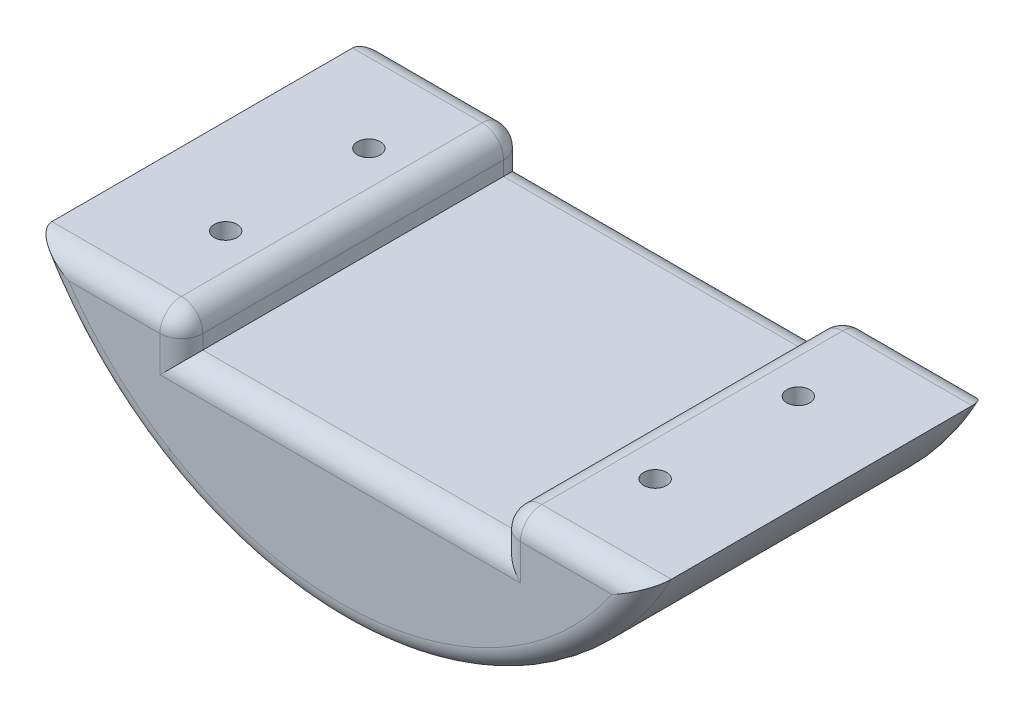
SolidWorks part; units mm, degrees
material "Pure Lead"
ref_plane "Front Plane" through (0, 0, 0) normal (0, 0, 1) x (1, 0, 0)
ref_plane "Top Plane" through (0, 0, 0) normal (0, 1, 0) x (1, 0, 0)
ref_plane "Right Plane" through (0, 0, 0) normal (1, 0, 0) x (0, 0, -1)
sketch "Sketch1" plane through (0, 0, 0) normal (0, 0, 1) x (1, 0, 0)
  line L0 (-46.6476, -15) -> (46.6476, -15)
  line L1 (-43.2666, -23) -> (43.2666, -23)
  line L2 (-33.9411, -28) -> (33.9411, -28)
  line L3 (-22.1811, -38) -> (-22.1811, -23)
  line L4 (-29.9539, -23) -> (-37.51, -23)
  line L5 (22.1811, -38) -> (22.1811, -23)
  line L6 (-22.1811, -38) -> (22.1811, -38)
  circle A0 centre (0, 0) radius 49
  circle A1 centre (0, 0) radius 44
  dimension "D1" = 8
  dimension "D2" = 98
  dimension "D3" = 88
  dimension "D4" = 15
  dimension "D5" = 5
  dimension "D8" = 10
extrude "Boss-Extrude1" add sketch "Sketch1" along normal blind 48 contours L6 A1 | A1 L1 A0 | L1 A1 L2 L3 | L2 A1 L3 | L2 A1 L1 L5 | L5 A1 L2 | L3 L6 L5 L2
sketch "Sketch2" plane through (0, -23, 0) normal (0, 1, 0) x (1, 0, 0)
  line L0 (-43.2666, -48) -> (-43.2666, 0) construction
  line L1 (-43.2666, -48) -> (-22.1811, -48) construction
  line L2 (-43.2666, -48) -> (-43.2666, 0) construction
  circle A0 centre (-29.9966, -14) radius 1.6
  circle A1 centre (-29.9966, -34) radius 1.6
  dimension "D1" = 20
  dimension "D2" = 13.27
  dimension "D3" = 14
  dimension "D4" = 13.27
extrude "Cut-Extrude1" cut sketch "Sketch2" against normal through all
sketch "Sketch3" plane through (0, -23, 0) normal (0, 1, 0) x (1, 0, 0)
  circle A0 centre (-29.9966, -14) radius 3.05
  circle A1 centre (-29.9966, -34) radius 3.05
extrude "Cut-Extrude2" cut sketch "Sketch3" along normal up to surface (20 mm away) from offset 25
mirror "Mirror1" about plane through (0, 0, 0) normal (1, 0, 0) of "Cut-Extrude2", "Cut-Extrude1"
fillet "Fillet1" radius 3 14 edges at (-22.1811, -25.5, 0) (-22.1811, -25.5, 48) (-32.7238, -23, 48) (-32.7238, -23, 0) (0, -49, 0) (0, -49, 48) (32.7238, -23, 48) (32.7238, -23, 0) (22.1811, -25.5, 0) (22.1811, -25.5, 48) (0, -28, 0) (0, -28, 48) (-22.1811, -23, 24) (22.1811, -23, 24)
